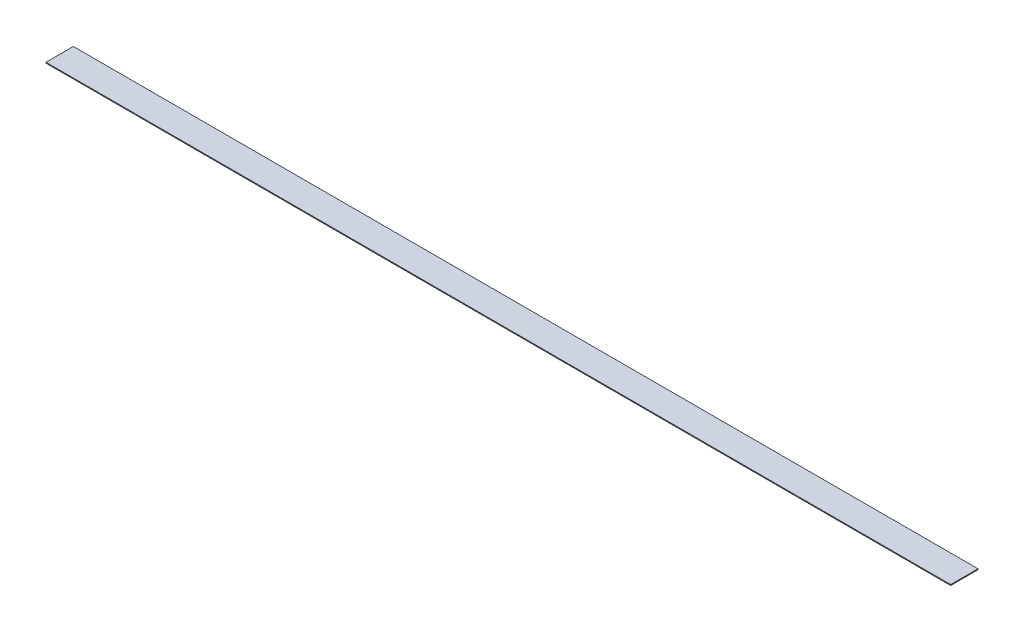
SolidWorks part; units mm, degrees
ref_plane "Front Plane" through (0, 0, 0) normal (0, 0, 1) x (1, 0, 0)
ref_plane "Top Plane" through (0, 0, 0) normal (0, 1, 0) x (1, 0, 0)
ref_plane "Right Plane" through (0, 0, 0) normal (1, 0, 0) x (0, 0, -1)
sketch "Sketch1" plane through (0, 0, 0) normal (0, 1, 0) x (1, 0, 0)
  line L1 (0, 0) -> (1682.75, 0)
  line L2 (0, 0) -> (0, 50.8)
  line L3 (0, 50.8) -> (1682.75, 50.8)
  line L4 (1682.75, 0) -> (1682.75, 50.8)
  dimension "D1" = 50.8
  dimension "D2" = 1682.75
extrude "Boss-Extrude1" add sketch "Sketch1" along normal blind 1.5875
